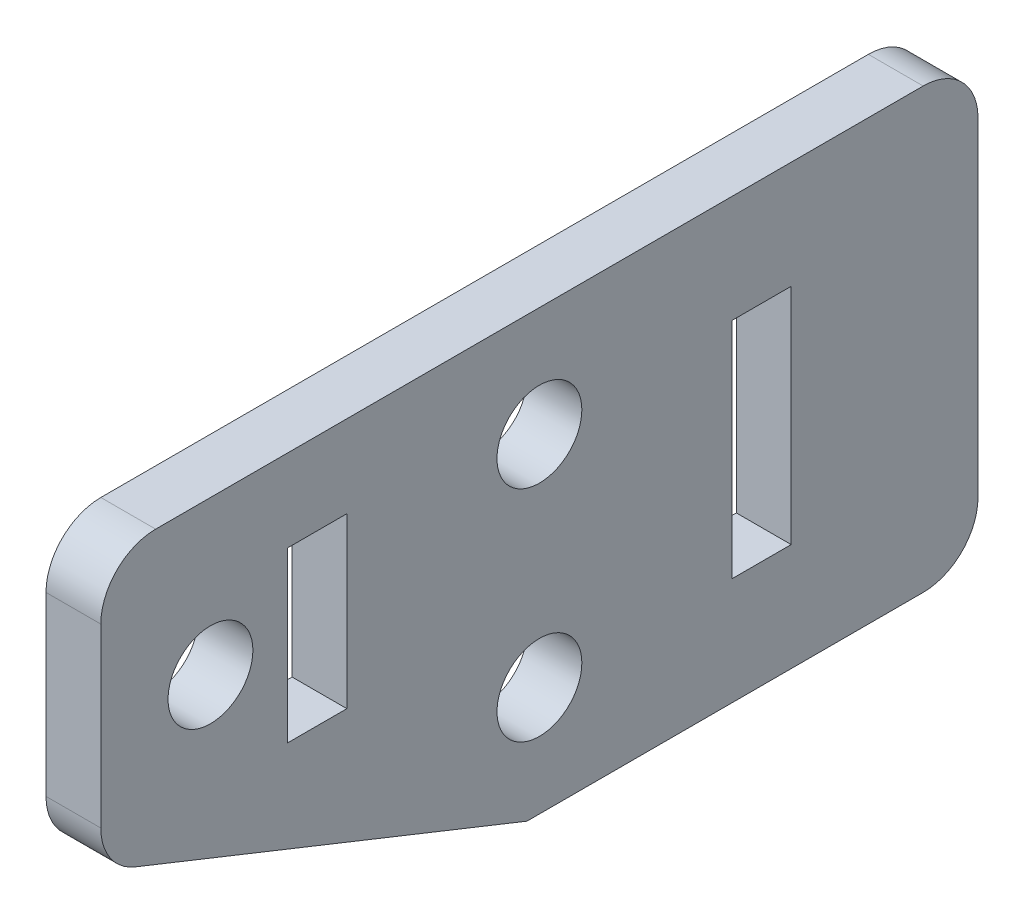
SolidWorks part; units mm, degrees
material "AISI 4130 Steel, annealed at 865C"
ref_plane "X-Y Datum" through (0, 0, 0) normal (0, 0, 1) x (1, 0, 0)
ref_plane "X-Z Datum" through (0, 0, 0) normal (0, 1, 0) x (1, 0, 0)
ref_plane "Y-Z Datum" through (0, 0, 0) normal (1, 0, 0) x (0, 0, -1)
sketch "Sketch2" plane through (0, 0, 0) normal (1, 0, 0) x (0, 0, -1)
  line L5 (-25.4, -12.7) -> (25.4, -12.7)
  line L6 (-25.4, -12.7) -> (-25.4, 12.7)
  line L7 (-25.4, 12.7) -> (25.4, 12.7)
  line L8 (25.4, -12.7) -> (25.4, 12.7)
  point P6 (-25.4, 0)
  point P8 (0, 12.7)
  dimension "D1" = 25.4
  dimension "D2" = 50.8
extrude "Boss-Extrude1" add sketch "Sketch2" along normal blind 3.175
sketch3d "3DSketch1"
  line L6 (0, 0, 0) -> (22.4872, 0, 0)
sketch "Sketch4" plane through (3.175, 0, 0) normal (1, 0, 0) x (0, 0, -1)
  line L2 (0, -12.987) -> (-25.4, -12.7)
  line L4 (0, -12.987) -> (-22.4038, -4.0507) construction
  line L5 (-22.4038, -4.0507) -> (-46.8524, 5.7013) construction
  line L6 (0, -12.987) -> (-22.4038, -4.0507)
  line L7 (-22.4038, -4.0507) -> (-46.8524, 5.7013)
  line L8 (-46.8524, 5.7013) -> (-46.8524, -12.7)
  line L9 (-46.8524, -12.7) -> (-25.4, -12.7)
extrude "Cut-Extrude2" cut sketch "Sketch4" against normal through all
fillet "Fillet2" radius 3.175 4 edges at (1.5875, -12.7, -25.4) (1.5875, 12.7, -25.4) (1.5875, 12.7, 25.4) (1.5875, -2.8555, 25.4)
sketch "Sketch5" plane through (3.175, 0, 0) normal (1, 0, 0) x (0, 0, -1)
  line L0 (0, 0) -> (0, 50000) construction
  line L1 (-14.5796, -1.8415) -> (-11.1506, -1.8415)
  line L2 (-14.5796, -1.8415) -> (-14.5796, 7.9375)
  line L3 (-14.5796, 7.9375) -> (-11.1506, 7.9375)
  line L4 (-11.1506, -1.8415) -> (-11.1506, 7.9375)
  line L5 (11.1506, -6.477) -> (14.5796, -6.477)
  line L6 (11.1506, -6.477) -> (11.1506, 6.477)
  line L7 (11.1506, 6.477) -> (14.5796, 6.477)
  line L8 (14.5796, -6.477) -> (14.5796, 6.477)
  line L9 (0, 0) -> (-50000, 0) construction
  line L10 (22.225, 12.7) -> (-22.225, 12.7) construction
  point P14 (11.1506, 0)
  dimension "D1" = 22.3012
  dimension "D2" = 11.1506
  dimension "D3" = 3.429
  dimension "D4" = 9.779
  dimension "D5" = 3.429
  dimension "D6" = 12.954
  dimension "D7" = 4.7625
extrude "Cut-Extrude3" cut sketch "Sketch5" against normal through all
hole_wizard "#10 (0.1935) Diameter Hole1" positions "Sketch6" profile "Sketch7" hole size "#10" standard "ANSI Inch" end condition through all
sketch "Sketch6" plane through (3.175, 0, 0) normal (1, 0, 0) x (0, 0, -1)
  point P0 (-19.05, 3.81)
  point P18 (0, -6.35)
  point P20 (0, 6.35)
  dimension "D1" = 6.35
  dimension "D2" = 12.7
  dimension "D3" = 19.05
  dimension "D4" = 3.81
sketch "Sketch7" plane through (3.175, 3.81, 19.05) normal (0, 1, 0) x (0, 0, -1)
  line L0 (0, 0) -> (0, 3.175)
  line L1 (0, 3.175) -> (2.4574, 3.175)
  line L2 (2.4574, 3.175) -> (2.4574, 0)
  line L5 (2.4574, 0) -> (0, 0)
  line L11 (0, -6.35) -> (0, 107.95) construction
  dimension "Thru Hole Dia." = 4.9149
  dimension "Thru Hole Depth" = 3.175
